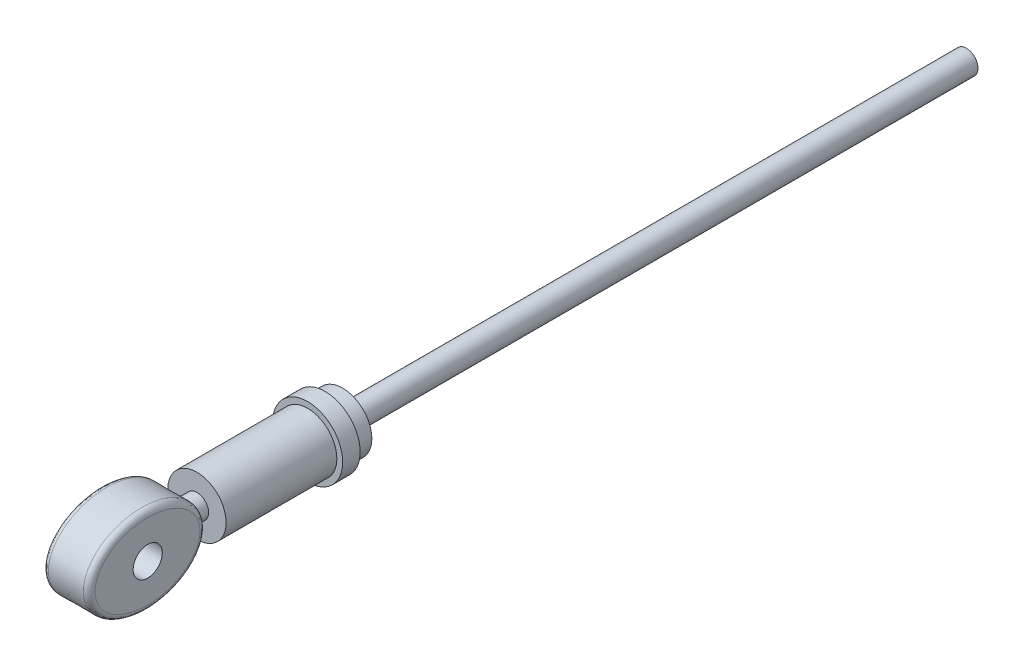
SolidWorks part; units mm, degrees
ref_plane "Front Plane" through (0, 0, 0) normal (0, 0, 1) x (1, 0, 0)
ref_plane "Top Plane" through (0, 0, 0) normal (0, 1, 0) x (1, 0, 0)
ref_plane "Right Plane" through (0, 0, 0) normal (1, 0, 0) x (0, 0, -1)
sketch "Sketch1" plane through (0, 0, 0) normal (0, 0, 1) x (1, 0, 0)
  circle A0 centre (0, 0) radius 5
  dimension "D1" = 10
extrude "Boss-Extrude1" add sketch "Sketch1" along normal blind 19
sketch "Sketch2" plane through (0, 0, 0) normal (0, 0, -1) x (-1, 0, 0)
  circle A0 centre (0, 0) radius 6
  dimension "D1" = 12
extrude "Boss-Extrude2" add sketch "Sketch2" along normal blind 3
sketch "Sketch3" plane through (0, 0, -3) normal (0, 0, -1) x (-1, 0, 0)
  circle A0 centre (0, 0) radius 5
  dimension "D1" = 10
extrude "Boss-Extrude3" add sketch "Sketch3" along normal blind 3
sketch "Sketch4" plane through (0, 0, -6) normal (0, 0, -1) x (-1, 0, 0)
  circle A0 centre (0, 0) radius 2
  dimension "D1" = 4
extrude "Boss-Extrude4" add sketch "Sketch4" along normal blind 107
sketch "Sketch5" plane through (0, 0, 0) normal (1, 0, 0) x (0, 0, -1)
  ellipse E0 centre (-31.4836, 0) end of major axis (-41.4836, 0) minor radius 7.5
  dimension "D1" = 15
extrude "Boss-Extrude5" add sketch "Sketch5" along normal mid plane 8 separate body
sketch "Sketch6" plane through (0, 0, 19) normal (0, 0, 1) x (1, 0, 0)
  circle A0 centre (0, 0) radius 2
  dimension "D1" = 4
extrude "Boss-Extrude6" add sketch "Sketch6" along normal blind 4
fillet "Fillet1" radius 1 2 edges at (-4, 0, 41.4836) (4, 0, 41.4836)
sketch "Sketch7" plane through (4, 0, 0) normal (1, 0, 0) x (0, 0, -1)
  circle A0 centre (-31.4449, 0) radius 2.5
  dimension "D1" = 5
extrude "Cut-Extrude1" cut sketch "Sketch7" against normal through all
